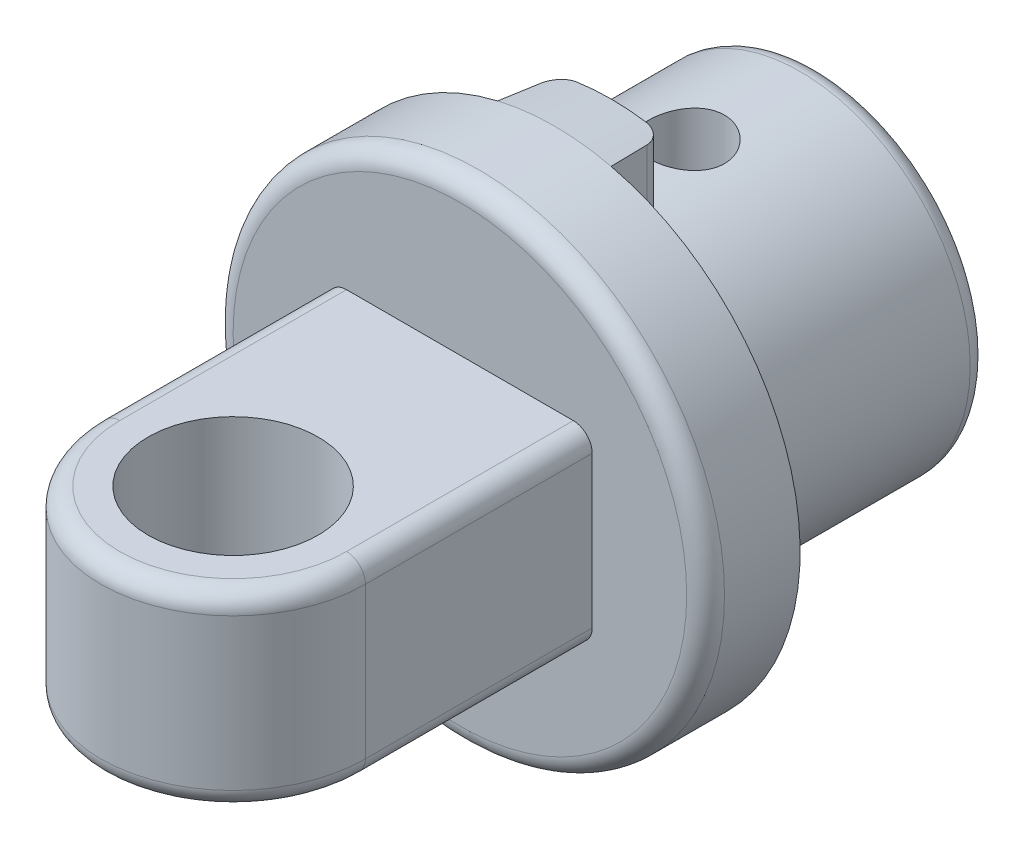
SolidWorks part; units mm, degrees
ref_plane "Plane1" through (0, 0, 0) normal (0, 0, 1) x (1, 0, 0)
ref_plane "Plane2" through (0, 0, 0) normal (0, 1, 0) x (1, 0, 0)
ref_plane "Plane3" through (0, 0, 0) normal (1, 0, 0) x (0, 0, -1)
sketch "Esquisse1" plane through (0, 0, 0) normal (0, 0, 1) x (1, 0, 0)
  circle A0 centre (0, 0) radius 4.5
  dimension "D1" = 9
extrude "Base-Extrusion" add sketch "Esquisse1" along normal blind 7
sketch "Esquisse2" plane through (0, 0, 7) normal (0, 0, 1) x (1, 0, 0)
  circle A0 centre (0, 0) radius 6.5
  dimension "D1" = 13
extrude "Boss.-Extru.1" add sketch "Esquisse2" along normal blind 2.5
sketch "Esquisse3" plane through (0, 0, 0) normal (0, 1, 0) x (1, 0, 0)
  line L0 (0, 0) -> (0, -14.4273) construction
  line L1 (0, -7) -> (0, 0) construction
  line L2 (-3.5, -9.5) -> (-3.5, -15.5)
  line L3 (3.5, -9.5) -> (3.5, -15.5)
  line L4 (-3.5, -15.5) -> (3.5, -15.5) construction
  line L5 (-3.5, -9.5) -> (3.5, -9.5)
  line L6 (-6.5, -9.5) -> (6.5, -9.5) construction
  arc A0 (-3.5, -15.5) -> (3.5, -15.5) centre (0, -15.5) ccw
  dimension "D1" = 3.5
  dimension "D2" = 6
  dimension "D3" = 6
extrude "Boss.-Extru.2" add sketch "Esquisse3" along normal mid plane 5
sketch "Esquisse4" plane through (0, 2.5, 0) normal (0, 1, 0) x (-1, 0, 0)
  line L0 (0, 15.5) -> (0, 3.5) construction
  line L3 (-6.5, 7) -> (6.5, 7) construction
  circle A0 centre (0, 15.5) radius 2.25
  circle A1 centre (0, 3.5) radius 1
  dimension "D1" = 4.5
  dimension "D2" = 2
  dimension "D3" = 3.5
extrude "Enlèv. mat.-Extru.1" cut sketch "Esquisse4" against normal mid plane 45
sketch "Esquisse5" plane through (0, 0, 7) normal (0, 0, -1) x (-1, 0, 0)
  line L0 (0, 0) -> (0, 10) construction
  line L1 (1.5, 6.3246) -> (1.5, 4)
  line L2 (-1.5, 6.3246) -> (-1.5, 4)
  line L3 (1.5, 4) -> (-1.5, 4)
  arc A0 (1.5, 6.3246) -> (-1.5, 6.3246) centre (0, 0) ccw
  dimension "D2" = 6.5
  dimension "D1" = 3
extrude "Boss.-Extru.3" add sketch "Esquisse5" along normal blind 1.5 draft 5
fillet "Congé1" radius 0.5
